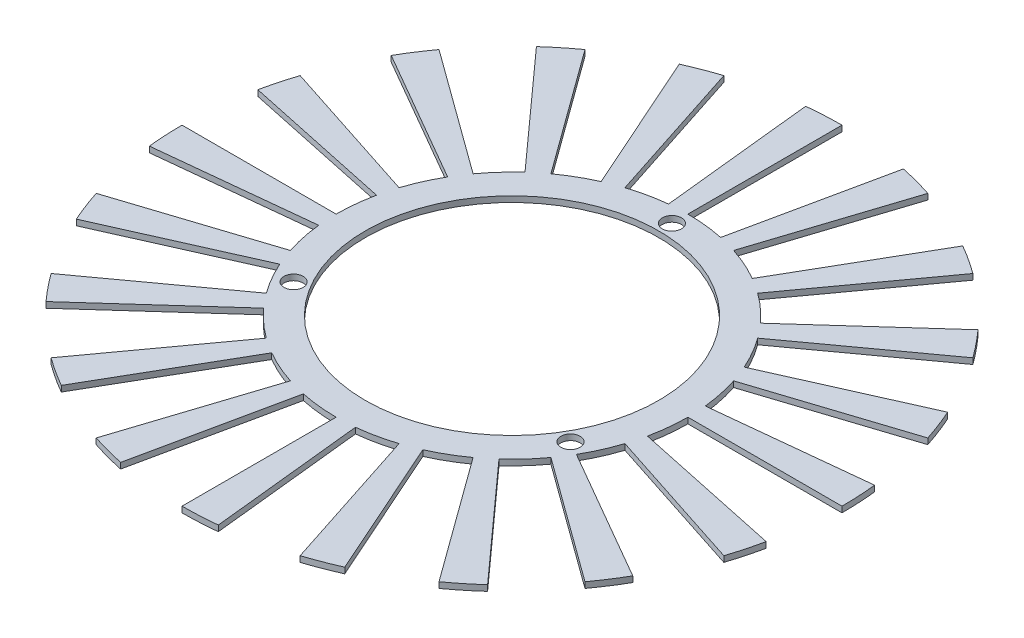
SolidWorks part; units mm, degrees
material "AISI 1010 Steel, hot rolled bar"
ref_plane "Front Plane" through (0, 0, 0) normal (0, 0, 1) x (1, 0, 0)
ref_plane "Top Plane" through (0, 0, 0) normal (0, 1, 0) x (1, 0, 0)
ref_plane "Right Plane" through (0, 0, 0) normal (1, 0, 0) x (0, 0, -1)
sketch "Sketch1" plane through (0, 0, 0) normal (0, 1, 0) x (1, 0, 0)
  circle A0 centre (0, 0) radius 25.25
  dimension "D1" = 50.5
extrude "Extrude-Thin1" add sketch "Sketch1" against normal blind 1 thin
sketch "Sketch2" plane through (0, 0, 0) normal (0, 1, 0) x (1, 0, 0)
  line L0 (0, -30.25) -> (0, 30.25) construction
  line L1 (0, 0) -> (23.8157, -13.75) construction
  line L2 (0, 0) -> (-23.8157, -13.75) construction
  circle A0 centre (0, 27.5) radius 1.65
  circle A1 centre (0, 0) radius 30.25 construction
  circle A4 centre (0, 0) radius 27.5 construction
  circle A7 centre (23.8157, -13.75) radius 1.65
  circle A8 centre (-23.8157, -13.75) radius 1.65
  dimension "D1" = 55
  dimension "D2" = 3.3
  dimension "D3" = 120
  dimension "D4" = 120
extrude "Cut-Extrude3" cut sketch "Sketch2" against normal blind 10
sketch "Sketch5" plane through (0, -1, 0) normal (0, -1, 0) x (1, 0, 0)
  line L0 (0, 0) -> (0, 35.9971) construction
  line L1 (0, 0) -> (3.5651, 33.9199) construction
  line L2 (0, 56.75) -> (0, 30.25)
  line L3 (3.162, 30.0843) -> (5.932, 56.4391)
  line L4 (17.5367, 53.9725) -> (9.3478, 28.7695)
  line L5 (12.3038, 27.6348) -> (23.0823, 51.8437)
  line L6 (33.3568, 45.9117) -> (17.7805, 24.4728)
  line L7 (20.2412, 22.4801) -> (37.9732, 42.1735)
  line L8 (45.9117, 33.3568) -> (24.4728, 17.7805)
  line L9 (26.1973, 15.125) -> (49.1469, 28.375)
  line L10 (53.9725, 17.5367) -> (28.7695, 9.3478)
  line L11 (29.589, 6.2893) -> (55.5099, 11.799)
  line L12 (56.75, 0) -> (30.25, 0)
  line L13 (30.0843, -3.162) -> (56.4391, -5.932)
  line L14 (53.9725, -17.5367) -> (28.7695, -9.3478)
  line L15 (27.6348, -12.3038) -> (51.8437, -23.0823)
  line L16 (45.9117, -33.3568) -> (24.4728, -17.7805)
  line L17 (22.4801, -20.2412) -> (42.1735, -37.9732)
  line L18 (33.3568, -45.9117) -> (17.7805, -24.4728)
  line L19 (15.125, -26.1973) -> (28.375, -49.1469)
  line L20 (17.5367, -53.9725) -> (9.3478, -28.7695)
  line L21 (6.2893, -29.589) -> (11.799, -55.5099)
  line L22 (0, -56.75) -> (0, -30.25)
  line L23 (-3.162, -30.0843) -> (-5.932, -56.4391)
  line L24 (-17.5367, -53.9725) -> (-9.3478, -28.7695)
  line L25 (-12.3038, -27.6348) -> (-23.0823, -51.8437)
  line L26 (-33.3568, -45.9117) -> (-17.7805, -24.4728)
  line L27 (-20.2412, -22.4801) -> (-37.9732, -42.1735)
  line L28 (-45.9117, -33.3568) -> (-24.4728, -17.7805)
  line L29 (-26.1973, -15.125) -> (-49.1469, -28.375)
  line L30 (-53.9725, -17.5367) -> (-28.7695, -9.3478)
  line L31 (-29.589, -6.2893) -> (-55.5099, -11.799)
  line L32 (-56.75, 0) -> (-30.25, 0)
  line L33 (-30.0843, 3.162) -> (-56.4391, 5.932)
  line L34 (-53.9725, 17.5367) -> (-28.7695, 9.3478)
  line L35 (-27.6348, 12.3038) -> (-51.8437, 23.0823)
  line L36 (-45.9117, 33.3568) -> (-24.4728, 17.7805)
  line L37 (-22.4801, 20.2412) -> (-42.1735, 37.9732)
  line L38 (-33.3568, 45.9117) -> (-17.7805, 24.4728)
  line L39 (-15.125, 26.1973) -> (-28.375, 49.1469)
  line L40 (-17.5367, 53.9725) -> (-9.3478, 28.7695)
  line L41 (-6.2893, 29.589) -> (-11.799, 55.5099)
  circle A0 centre (0, 0) radius 30.25 construction
  arc A1 (3.162, 30.0843) -> (0, 30.25) centre (0, 0) ccw
  arc A2 (5.932, 56.4391) -> (0, 56.75) centre (0, 0) ccw
  arc A3 (23.0823, 51.8437) -> (17.5367, 53.9725) centre (0, 0) ccw
  arc A4 (12.3038, 27.6348) -> (9.3478, 28.7695) centre (0, 0) ccw
  arc A5 (37.9732, 42.1735) -> (33.3568, 45.9117) centre (0, 0) ccw
  arc A6 (20.2412, 22.4801) -> (17.7805, 24.4728) centre (0, 0) ccw
  arc A7 (49.1469, 28.375) -> (45.9117, 33.3568) centre (0, 0) ccw
  arc A8 (26.1973, 15.125) -> (24.4728, 17.7805) centre (0, 0) ccw
  arc A9 (55.5099, 11.799) -> (53.9725, 17.5367) centre (0, 0) ccw
  arc A10 (29.589, 6.2893) -> (28.7695, 9.3478) centre (0, 0) ccw
  arc A11 (56.4391, -5.932) -> (56.75, 0) centre (0, 0) ccw
  arc A12 (30.0843, -3.162) -> (30.25, 0) centre (0, 0) ccw
  arc A13 (51.8437, -23.0823) -> (53.9725, -17.5367) centre (0, 0) ccw
  arc A14 (27.6348, -12.3038) -> (28.7695, -9.3478) centre (0, 0) ccw
  arc A15 (42.1735, -37.9732) -> (45.9117, -33.3568) centre (0, 0) ccw
  arc A16 (22.4801, -20.2412) -> (24.4728, -17.7805) centre (0, 0) ccw
  arc A17 (28.375, -49.1469) -> (33.3568, -45.9117) centre (0, 0) ccw
  arc A18 (15.125, -26.1973) -> (17.7805, -24.4728) centre (0, 0) ccw
  arc A19 (11.799, -55.5099) -> (17.5367, -53.9725) centre (0, 0) ccw
  arc A20 (6.2893, -29.589) -> (9.3478, -28.7695) centre (0, 0) ccw
  arc A21 (-5.932, -56.4391) -> (0, -56.75) centre (0, 0) ccw
  arc A22 (-3.162, -30.0843) -> (0, -30.25) centre (0, 0) ccw
  arc A23 (-23.0823, -51.8437) -> (-17.5367, -53.9725) centre (0, 0) ccw
  arc A24 (-12.3038, -27.6348) -> (-9.3478, -28.7695) centre (0, 0) ccw
  arc A25 (-37.9732, -42.1735) -> (-33.3568, -45.9117) centre (0, 0) ccw
  arc A26 (-20.2412, -22.4801) -> (-17.7805, -24.4728) centre (0, 0) ccw
  arc A27 (-49.1469, -28.375) -> (-45.9117, -33.3568) centre (0, 0) ccw
  arc A28 (-26.1973, -15.125) -> (-24.4728, -17.7805) centre (0, 0) ccw
  arc A29 (-55.5099, -11.799) -> (-53.9725, -17.5367) centre (0, 0) ccw
  arc A30 (-29.589, -6.2893) -> (-28.7695, -9.3478) centre (0, 0) ccw
  arc A31 (-56.4391, 5.932) -> (-56.75, 0) centre (0, 0) ccw
  arc A32 (-30.0843, 3.162) -> (-30.25, 0) centre (0, 0) ccw
  arc A33 (-51.8437, 23.0823) -> (-53.9725, 17.5367) centre (0, 0) ccw
  arc A34 (-27.6348, 12.3038) -> (-28.7695, 9.3478) centre (0, 0) ccw
  arc A35 (-42.1735, 37.9732) -> (-45.9117, 33.3568) centre (0, 0) ccw
  arc A36 (-22.4801, 20.2412) -> (-24.4728, 17.7805) centre (0, 0) ccw
  arc A37 (-28.375, 49.1469) -> (-33.3568, 45.9117) centre (0, 0) ccw
  arc A38 (-15.125, 26.1973) -> (-17.7805, 24.4728) centre (0, 0) ccw
  arc A39 (-11.799, 55.5099) -> (-17.5367, 53.9725) centre (0, 0) ccw
  arc A40 (-6.2893, 29.589) -> (-9.3478, 28.7695) centre (0, 0) ccw
  point P87 (0, 0)
  dimension "D2" = 26.5
  dimension "D1" = 6
  dimension "D3" = 20
extrude "Boss-Extrude1" add sketch "Sketch5" against normal blind 1
